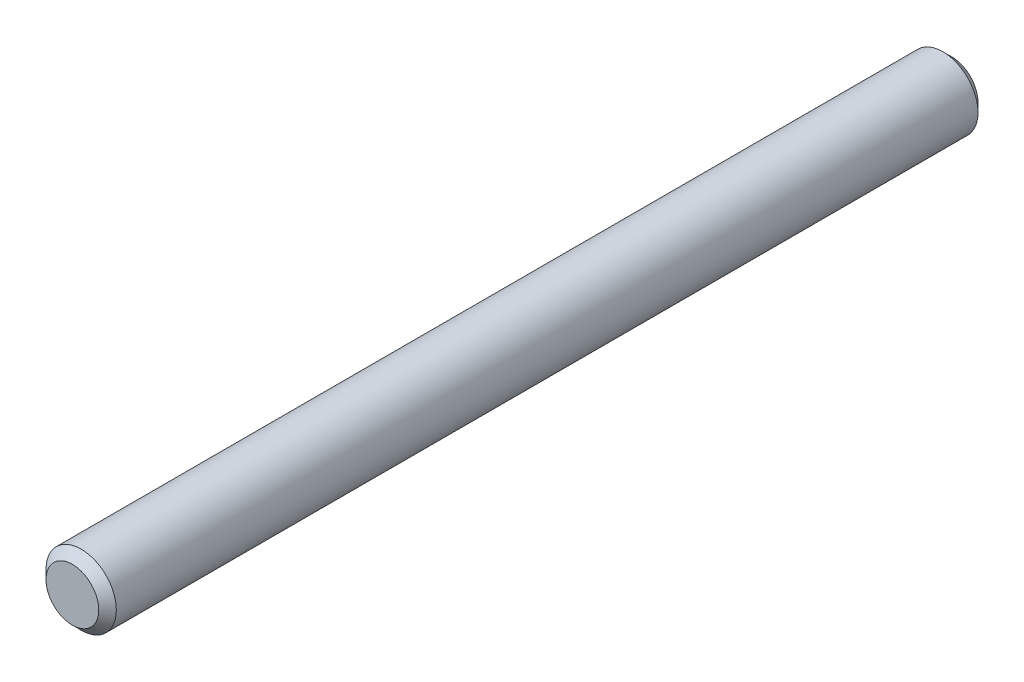
SolidWorks part; units mm, degrees
ref_plane "Front Plane" through (0, 0, 0) normal (0, 0, 1) x (1, 0, 0)
ref_plane "Top Plane" through (0, 0, 0) normal (0, 1, 0) x (1, 0, 0)
ref_plane "Right Plane" through (0, 0, 0) normal (1, 0, 0) x (0, 0, -1)
sketch "Sketch1" plane through (0, 0, 0) normal (0, 0, 1) x (1, 0, 0)
  circle A0 centre (0, 0) radius 2
  dimension "D1" = 4
extrude "Boss-Extrude1" add sketch "Sketch1" along normal mid plane 50
chamfer "Chamfer1" distance 0.5 angle 45 2 edges at (2, 0, -25) (2, 0, 25)
